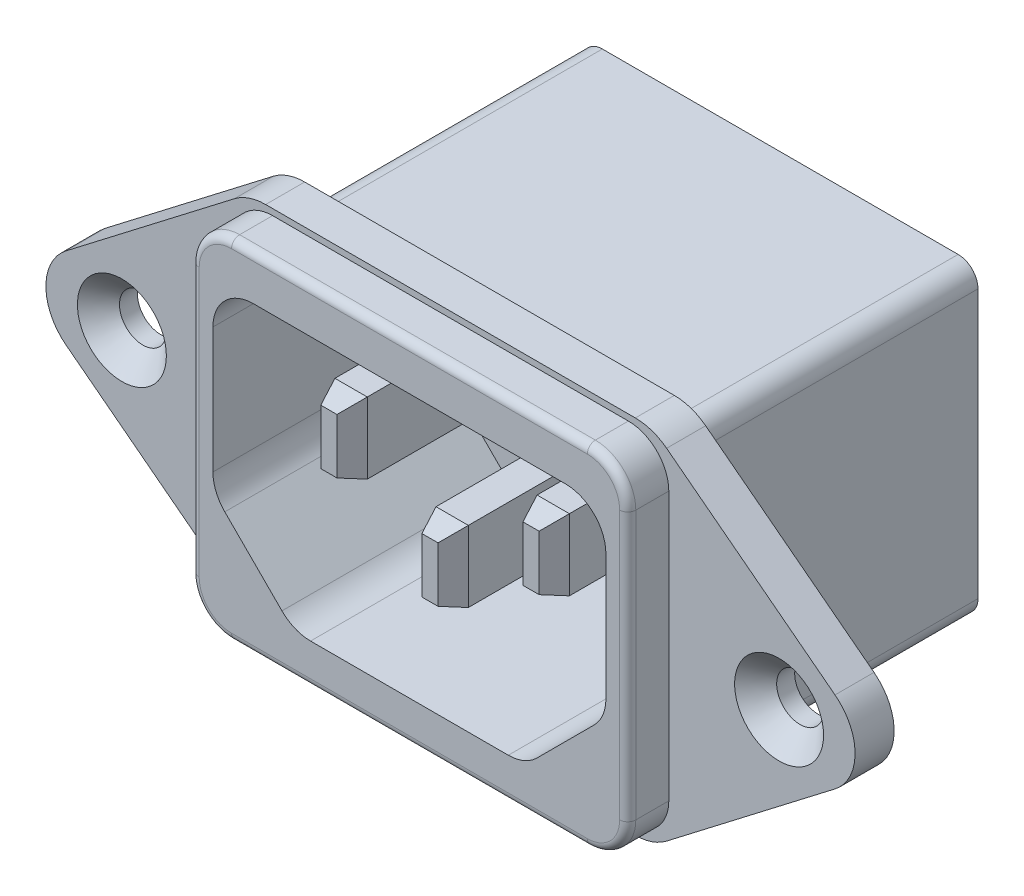
SolidWorks part; units mm, degrees
ref_plane "Front Plane" through (0, 0, 0) normal (0, 0, 1) x (1, 0, 0)
ref_plane "Top Plane" through (0, 0, 0) normal (0, 1, 0) x (1, 0, 0)
ref_plane "Right Plane" through (0, 0, 0) normal (1, 0, 0) x (0, 0, -1)
sketch "Sketch1" plane through (0, 0, 0) normal (0, 0, 1) x (1, 0, 0)
  line L0 (0, 0) -> (0, 20.1251) construction
  line L1 (-13.6, 17) -> (13.6, 17)
  line L3 (-13.6, -17) -> (13.6, -17)
  line L5 (-21.4292, -1.3416) -> (-13.6, -17)
  line L6 (18, 0) -> (0, 0) construction
  line L7 (21.4292, -1.3416) -> (13.6, -17)
  line L8 (-13.6, 17) -> (-21.4292, 1.3416)
  line L9 (13.6, 17) -> (21.4292, 1.3416)
  arc A2 (-21.4292, -1.3416) -> (-21.4292, 1.3416) centre (-18.7459, 0) cw
  arc A3 (21.4292, -1.3416) -> (21.4292, 1.3416) centre (18.7459, 0) ccw
  point P2 (-22.1, 0)
  point P18 (22.1, 0)
  dimension "D7" = 3
  dimension "D1" = 34
  dimension "D2" = 44.2
  dimension "D3" = 27.2
  dimension "D6" = 116.565
extrude "Extrude1" add sketch "Sketch1" against normal blind 5.15
fillet "Fillet1" radius 1 4 edges at (-13.6, -17, -2.575) (13.6, -17, -2.575) (13.6, 17, -2.575) (-13.6, 17, -2.575)
sketch "Sketch2" plane through (0, 0, -5.15) normal (0, 0, -1) x (-1, 0, 0)
  line L0 (0, 0) -> (0, 5.108) construction
  line L1 (-12.9, 15.65) -> (12.9, 15.65)
  line L2 (-13.9, 14.65) -> (-13.9, -14.65)
  line L3 (-12.9, -15.65) -> (12.9, -15.65)
  line L4 (13.9, 14.65) -> (13.9, -14.65)
  line L5 (0, 5.108) -> (4.8178, 0) construction
  line L6 (4.8178, 0) -> (0, 0) construction
  arc A0 (-12.9, 15.65) -> (-13.9, 14.65) centre (-12.9, 14.65) ccw
  arc A1 (12.9, 15.65) -> (13.9, 14.65) centre (12.9, 14.65) cw
  arc A2 (12.9, -15.65) -> (13.9, -14.65) centre (12.9, -14.65) ccw
  arc A3 (-13.9, -14.65) -> (-12.9, -15.65) centre (-12.9, -14.65) ccw
  dimension "D3" = 1
  dimension "D1" = 27.8
  dimension "D2" = 31.3
extrude "Extrude2" add sketch "Sketch2" along normal blind 17.78
sketch "Sketch3" plane through (0, 0, 0) normal (0, 0, 1) x (1, 0, 0)
  line L0 (0, 0) -> (0, 5.1467) construction
  line L1 (0, 5.1467) -> (2.496, 0) construction
  line L2 (2.496, 0) -> (0, 0) construction
  line L3 (-12.15, -9.18) -> (-7.15, -14.18)
  line L4 (-12.15, 2.12) -> (12.15, 2.12)
  line L5 (-12.15, 2.12) -> (-12.15, -9.18)
  line L6 (-7.15, -14.18) -> (7.15, -14.18)
  line L7 (12.15, 2.12) -> (12.15, -9.18)
  line L8 (7.15, -14.18) -> (12.15, -9.18)
  line L9 (-12.982, -17) -> (12.982, -17) construction
  point P5 (12.15, -14.18)
  point P6 (-12.15, -14.18)
  dimension "D1" = 16.3
  dimension "D2" = 24.3
  dimension "D5" = 2.82
extrude "Extrude3" cut sketch "Sketch3" against normal blind 13.97
sketch "Sketch4" plane through (0, 0, 0) normal (0, 0, 1) x (1, 0, 0)
  line L0 (0, 0) -> (0, -16.7014) construction
  line L1 (-11, 4.8886) -> (11, 4.8886)
  line L2 (-13.5, 2.3886) -> (-13.5, -14.2014)
  line L3 (-11, -16.7014) -> (11, -16.7014)
  line L4 (13.5, 2.3886) -> (13.5, -14.2014)
  line L6 (-21.4292, -1.3416) -> (-13.8764, -16.4472)
  line L7 (-12.982, -17) -> (12.982, -17)
  line L8 (-21.4292, -1.3416) -> (-13.8764, -16.4472)
  line L9 (13.8764, -16.4472) -> (21.4292, -1.3416)
  line L10 (12.982, 17) -> (-12.982, 17)
  line L11 (13.8764, -16.4472) -> (21.4292, -1.3416)
  line L13 (-12.982, -17) -> (12.982, -17)
  line L14 (12.15, 2.12) -> (-12.15, 2.12) construction
  line L16 (12.982, 17) -> (-12.982, 17)
  line L19 (21.4292, 1.3416) -> (13.8764, 16.4472)
  line L20 (21.4292, 1.3416) -> (13.8764, 16.4472)
  line L21 (-13.8764, 16.4472) -> (-21.4292, 1.3416)
  line L22 (-13.8764, 16.4472) -> (-21.4292, 1.3416)
  arc A0 (-13.5, 2.3886) -> (-11, 4.8886) centre (-11, 2.3886) cw
  arc A1 (13.5, 2.3886) -> (11, 4.8886) centre (11, 2.3886) ccw
  arc A2 (13.5, -14.2014) -> (11, -16.7014) centre (11, -14.2014) cw
  arc A3 (-13.5, -14.2014) -> (-11, -16.7014) centre (-11, -14.2014) ccw
  arc A10 (-13.8764, -16.4472) -> (-12.982, -17) centre (-12.982, -16) ccw
  arc A11 (-13.8764, -16.4472) -> (-12.982, -17) centre (-12.982, -16) ccw
  arc A12 (12.982, -17) -> (13.8764, -16.4472) centre (12.982, -16) ccw
  arc A13 (12.982, -17) -> (13.8764, -16.4472) centre (12.982, -16) ccw
  arc A14 (21.4292, -1.3416) -> (21.4292, 1.3416) centre (18.7459, 0) ccw
  arc A15 (21.4292, -1.3416) -> (21.4292, 1.3416) centre (18.7459, 0) ccw
  arc A16 (13.8764, 16.4472) -> (12.982, 17) centre (12.982, 16) ccw
  arc A17 (13.8764, 16.4472) -> (12.982, 17) centre (12.982, 16) ccw
  arc A18 (-12.982, 17) -> (-13.8764, 16.4472) centre (-12.982, 16) ccw
  arc A19 (-12.982, 17) -> (-13.8764, 16.4472) centre (-12.982, 16) ccw
  arc A20 (-21.4292, 1.3416) -> (-21.4292, -1.3416) centre (-18.7459, 0) ccw
  arc A21 (-21.4292, 1.3416) -> (-21.4292, -1.3416) centre (-18.7459, 0) ccw
  dimension "D5" = 2.5
  dimension "D2" = 27
  dimension "D3" = 21.59
  dimension "D4" = 2.7686
  dimension "D1" = 0
extrude "Extrude4" cut sketch "Sketch4" against normal blind 3.81
fillet "Fillet2" radius 2.5 6 edges at (-7.15, -14.18, -6.985) (-12.15, -9.18, -6.985) (-12.15, 2.12, -6.985) (12.15, 2.12, -6.985) (12.15, -9.18, -6.985) (7.15, -14.18, -6.985)
sketch "Sketch5" plane through (0, 0, -13.97) normal (0, 0, 1) x (1, 0, 0)
  line L0 (0, 0) -> (0, -10.15) construction
  line L1 (-12.982, -17) -> (12.982, -17) construction
  line L2 (-7.25, -2) -> (-5.25, -2)
  line L3 (-7.25, -2) -> (-7.25, -6.4)
  line L4 (-7.25, -6.4) -> (-5.25, -6.4)
  line L5 (-5.25, -2) -> (-5.25, -6.4)
  line L6 (-1, -5.75) -> (1, -5.75)
  line L7 (-1, -5.75) -> (-1, -10.15)
  line L8 (-1, -10.15) -> (1, -10.15)
  line L9 (1, -5.75) -> (1, -10.15)
  line L10 (7.25, -6.4) -> (5.25, -6.4)
  line L11 (7.25, -2) -> (7.25, -6.4)
  line L12 (5.25, -2) -> (5.25, -6.4)
  line L13 (7.25, -2) -> (5.25, -2)
  dimension "D1" = 2
  dimension "D2" = 4.4
  dimension "D3" = 11.25
  dimension "D4" = 15
  dimension "D5" = 14.5
extrude "Extrude5" add sketch "Sketch5" along normal blind 12.7
chamfer "Chamfer1" distance 0.5 angle 70 6 edges at (6.25, -6.4, -1.27) (6.25, -2, -1.27) (0, -10.15, -1.27) (0, -5.75, -1.27) (-6.25, -6.4, -1.27) (-6.25, -2, -1.27)
chamfer "Chamfer2" distance 0.5 angle 70 6 edges at (7.25, -4.2, -1.27) (5.25, -4.2, -1.27) (1, -7.95, -1.27) (-1, -7.95, -1.27) (-7.25, -4.2, -1.27) (-5.25, -4.2, -1.27)
fillet "Fillet3" radius 0.5 8 edges at (12.7678, 4.1564, 0) (13.5, -5.9064, 0) (12.7678, -15.9692, 0) (0, -16.7014, 0) (-12.7678, -15.9692, 0) (-13.5, -5.9064, 0) (-12.7678, 4.1564, 0) (0, 4.8886, 0)
sketch "Sketch10" plane through (0, 0, -3.81) normal (0, 0, 1) x (1, 0, 0)
  line L0 (-13.5, 2.3886) -> (-13.5, -14.2014) construction
  line L1 (-11, -16.7014) -> (11, -16.7014) construction
  line L2 (11, 4.8886) -> (-11, 4.8886) construction
  line L3 (13.5, -14.2014) -> (13.5, 2.3886) construction
  line L4 (-13.5, 2.3886) -> (-13.5, -14.2014)
  line L5 (-11, -16.7014) -> (11, -16.7014)
  line L6 (11, 4.8886) -> (-11, 4.8886)
  line L7 (13.5, -14.2014) -> (13.5, 2.3886)
  arc A0 (-11, 4.8886) -> (-13.5, 2.3886) centre (-11, 2.3886) ccw construction
  arc A1 (-13.5, -14.2014) -> (-11, -16.7014) centre (-11, -14.2014) ccw construction
  arc A2 (11, -16.7014) -> (13.5, -14.2014) centre (11, -14.2014) ccw construction
  arc A3 (13.5, 2.3886) -> (11, 4.8886) centre (11, 2.3886) ccw construction
  arc A4 (-11, 4.8886) -> (-13.5, 2.3886) centre (-11, 2.3886) ccw
  arc A5 (-13.5, -14.2014) -> (-11, -16.7014) centre (-11, -14.2014) ccw
  arc A6 (11, -16.7014) -> (13.5, -14.2014) centre (11, -14.2014) ccw
  arc A7 (13.5, 2.3886) -> (11, 4.8886) centre (11, 2.3886) ccw
extrude "Extrude10" cut sketch "Sketch10" against normal through all flip side to cut
ref_plane "Plane1" through (0, 0, -2.54) normal (0, 0, 1) x (1, 0, 0)
sketch "Sketch11" plane through (0, 0, -2.54) normal (0, 0, 1) x (1, 0, 0)
  line L12 (-11, -15.4314) -> (11, -15.4314)
  line L13 (-12.23, 2.3886) -> (-12.23, -14.2014)
  line L14 (11, 3.6186) -> (-11, 3.6186)
  line L15 (12.23, -14.2014) -> (12.23, 2.3886)
  line L16 (-11, -15.4314) -> (11, -15.4314)
  line L17 (-12.23, 2.3886) -> (-12.23, -14.2014)
  line L18 (11, 3.6186) -> (-11, 3.6186)
  line L19 (12.23, -14.2014) -> (12.23, 2.3886)
  arc A12 (-12.23, -14.2014) -> (-11, -15.4314) centre (-11, -14.2014) ccw
  arc A13 (-11, 3.6186) -> (-12.23, 2.3886) centre (-11, 2.3886) ccw
  arc A14 (11, -15.4314) -> (12.23, -14.2014) centre (11, -14.2014) ccw
  arc A15 (12.23, 2.3886) -> (11, 3.6186) centre (11, 2.3886) ccw
  arc A16 (-12.23, -14.2014) -> (-11, -15.4314) centre (-11, -14.2014) ccw
  arc A17 (-11, 3.6186) -> (-12.23, 2.3886) centre (-11, 2.3886) ccw
  arc A18 (11, -15.4314) -> (12.23, -14.2014) centre (11, -14.2014) ccw
  arc A19 (12.23, 2.3886) -> (11, 3.6186) centre (11, 2.3886) ccw
  dimension "D1" = 1.27
extrude "Extrude11" cut sketch "Sketch11" against normal through all flip side to cut
sketch "Sketch12" plane through (0, 0, -2.54) normal (0, 0, -1) x (-1, 0, 0)
  line L0 (-11.43, 5.2696) -> (11.43, 5.2696)
  line L1 (13.3643, 4.6123) -> (23.7783, -3.3887)
  line L2 (23.7783, -8.4241) -> (13.3643, -16.4251)
  line L3 (11.43, -17.0824) -> (-11.43, -17.0824)
  line L4 (27.0554, -5.9064) -> (13.5, -5.9064) construction
  line L5 (13.5, -14.2014) -> (13.5, 2.3886) construction
  line L6 (0, 0) -> (0, 14.127) construction
  line L7 (-23.7783, -8.4241) -> (-13.3643, -16.4251)
  line L8 (-13.3643, 4.6123) -> (-23.7783, -3.3887)
  line L9 (12.23, 2.3886) -> (12.23, -14.2014) construction
  line L10 (11, -15.4314) -> (-11, -15.4314) construction
  line L11 (-12.23, -14.2014) -> (-12.23, 2.3886) construction
  line L12 (-11, 3.6186) -> (11, 3.6186) construction
  line L13 (12.23, 2.3886) -> (12.23, -14.2014)
  line L14 (11, -15.4314) -> (-11, -15.4314)
  line L15 (-12.23, -14.2014) -> (-12.23, 2.3886)
  line L16 (-11, 3.6186) -> (11, 3.6186)
  arc A0 (23.7783, -8.4241) -> (23.7783, -3.3887) centre (21.844, -5.9064) ccw
  arc A1 (11.43, 5.2696) -> (13.3643, 4.6123) centre (11.43, 2.0946) cw
  arc A2 (11.43, -17.0824) -> (13.3643, -16.4251) centre (11.43, -13.9074) ccw
  arc A3 (-11.43, -17.0824) -> (-13.3643, -16.4251) centre (-11.43, -13.9074) cw
  arc A4 (-23.7783, -8.4241) -> (-23.7783, -3.3887) centre (-21.844, -5.9064) cw
  arc A5 (-11.43, 5.2696) -> (-13.3643, 4.6123) centre (-11.43, 2.0946) ccw
  arc A6 (12.23, 2.3886) -> (11, 3.6186) centre (11, 2.3886) ccw construction
  arc A7 (11, -15.4314) -> (12.23, -14.2014) centre (11, -14.2014) ccw construction
  arc A8 (-12.23, -14.2014) -> (-11, -15.4314) centre (-11, -14.2014) ccw construction
  arc A9 (-11, 3.6186) -> (-12.23, 2.3886) centre (-11, 2.3886) ccw construction
  arc A10 (12.23, 2.3886) -> (11, 3.6186) centre (11, 2.3886) ccw
  arc A11 (11, -15.4314) -> (12.23, -14.2014) centre (11, -14.2014) ccw
  arc A12 (-12.23, -14.2014) -> (-11, -15.4314) centre (-11, -14.2014) ccw
  arc A13 (-11, 3.6186) -> (-12.23, 2.3886) centre (-11, 2.3886) ccw
  point P16 (12.5088, 5.2696)
  point P19 (12.5088, -17.0824)
  point P21 (0, -17.0824)
  point P29 (0, 5.2696)
  dimension "D1" = 3.175
  dimension "D2" = 50.038
  dimension "D3" = 22.352
  dimension "D4" = 11.43
extrude "Extrude12" add sketch "Sketch12" along normal blind 2.413
hole_wizard "CSK for M2.5 Flat Head Machine Screw1" positions "Sketch14" profile "Sketch13" countersink size "M2.5" standard "Ansi Metric" end condition through all
sketch "Sketch14" plane through (0, 0, -2.54) normal (0, 0, 1) x (1, 0, 0)
  line L0 (20.32, -5.9064) -> (13.5, -5.9064) construction
  line L1 (13.5, 2.3886) -> (13.5, -14.2014) construction
  line L2 (13.5, 2.3886) -> (13.5, -14.2014) construction
  point P0 (-20.32, -5.9064)
  point P1 (20.32, -5.9064)
  dimension "D1" = 20.32
  dimension "D2" = 40.64
sketch "Sketch13" plane through (-20.32, -5.9064, -2.54) normal (1, 0, 0) x (0, -1, 0)
  line L0 (0, 0) -> (0, 20.39)
  line L1 (0, 20.39) -> (1.45, 20.39)
  line L2 (1.45, 20.39) -> (1.45, 1.3)
  line L3 (1.45, 1.3) -> (2.75, 0)
  line L5 (2.75, 0) -> (0, 0)
  line L6 (-1.45, 1.3) -> (-2.75, 0) construction
  line L11 (0, -6.35) -> (0, 107.95) construction
  dimension "Thru Hole Dia." = 2.9
  dimension "Thru Hole Depth" = 20.39
  dimension "Near C'Sink Dia." = 5.5
  dimension "Near C'Sink Angle" = 90
